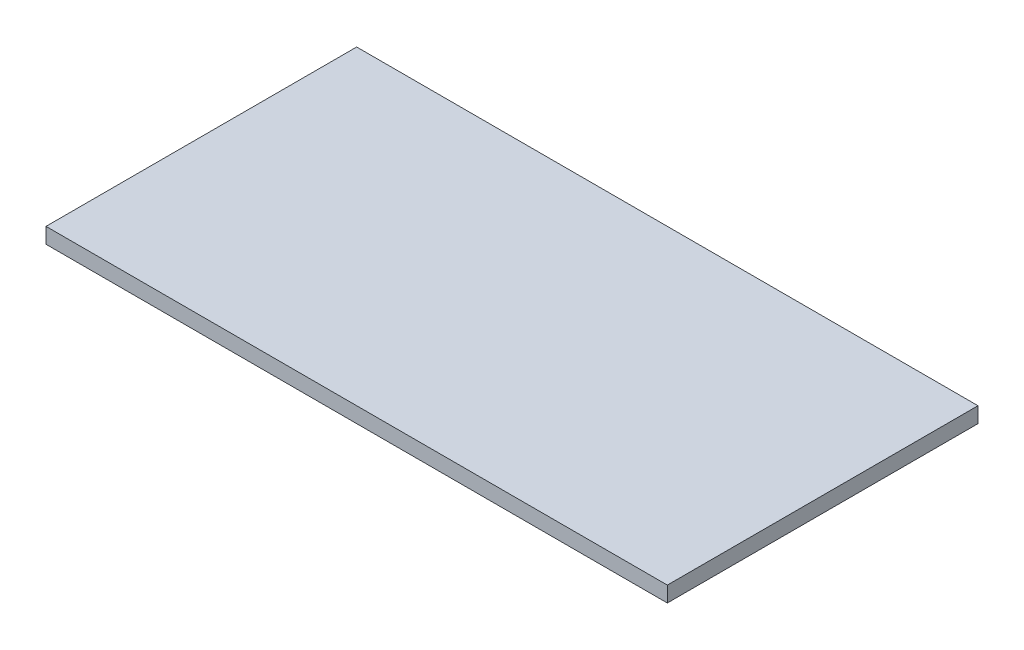
SolidWorks part; units mm, degrees
ref_plane "Front Plane" through (0, 0, 0) normal (0, 0, 1) x (1, 0, 0)
ref_plane "Top Plane" through (0, 0, 0) normal (0, 1, 0) x (1, 0, 0)
ref_plane "Right Plane" through (0, 0, 0) normal (1, 0, 0) x (0, 0, -1)
sketch "Sketch1" plane through (0, 0, 0) normal (0, 1, 0) x (1, 0, 0)
  line L1 (127, -63.5) -> (-127, -63.5)
  line L2 (127, -63.5) -> (127, 63.5)
  line L3 (127, 63.5) -> (-127, 63.5)
  line L4 (-127, -63.5) -> (-127, 63.5)
  line L5 (127, -63.5) -> (-127, 63.5) construction
  line L6 (127, 63.5) -> (-127, -63.5) construction
  point P0 (0, 0)
  dimension "D1" = 127
  dimension "D2" = 254
extrude "Boss-Extrude1" add sketch "Sketch1" along normal blind 6.35
sketch "Sketch2" plane through (0, 0, 0) normal (0, 1, 0) x (1, 0, 0)
  line L0 (-127, 0) -> (127, 0) construction
  line L1 (-127, 63.5) -> (-127, -63.5) construction
  line L2 (127, -63.5) -> (127, 63.5) construction
  line L3 (0, 63.5) -> (0, -63.5) construction
  line L4 (127, 63.5) -> (-127, 63.5) construction
  line L5 (-127, -63.5) -> (127, -63.5) construction
  line L6 (-107.95, -63.5) -> (-107.95, -57.15)
  line L7 (-127, -50.8) -> (-120.65, -50.8)
  line L8 (-9.398, -63.5) -> (-9.398, -57.15)
  line L9 (-127, 50.8) -> (-120.65, 50.8)
  line L10 (-120.65, -50.8) -> (-120.65, -57.15)
  line L11 (-120.65, -57.15) -> (-107.95, -57.15)
  line L12 (-107.95, 63.5) -> (-107.95, 57.15)
  line L13 (-120.65, 57.15) -> (-107.95, 57.15)
  line L14 (-120.65, 57.15) -> (-120.65, 50.8)
  line L15 (-9.398, 63.5) -> (-9.398, 57.15)
  line L16 (9.398, 63.5) -> (9.398, 57.15)
  line L17 (9.398, -63.5) -> (9.398, -57.15)
  line L18 (107.95, -63.5) -> (107.95, -57.15)
  line L19 (120.65, -57.15) -> (107.95, -57.15)
  line L20 (120.65, -50.8) -> (120.65, -57.15)
  line L21 (127, -50.8) -> (120.65, -50.8)
  line L22 (127, 50.8) -> (120.65, 50.8)
  line L23 (107.95, 63.5) -> (107.95, 57.15)
  line L24 (120.65, 57.15) -> (120.65, 50.8)
  line L25 (120.65, 57.15) -> (107.95, 57.15)
  line L26 (-9.398, -57.15) -> (9.398, -57.15)
  line L27 (-9.398, 57.15) -> (9.398, 57.15)
  line L28 (-51.5722, 5.2394) -> (-23.4255, 5.2394)
  line L33 (-63.2415, -5.2394) -> (-51.5722, 5.2394) construction
  line L34 (-63.2415, 5.2394) -> (-51.5722, -5.2394) construction
  line L35 (-51.5722, -5.2394) -> (-23.4255, -5.2394)
  line L36 (-63.2415, -5.2394) -> (-91.3883, -5.2394)
  line L37 (-63.2415, 5.2394) -> (-91.3883, 5.2394)
  line L38 (-63.2415, -5.2394) -> (-63.2415, -33.8843)
  line L39 (-51.5722, -5.2394) -> (-51.5722, -33.8843)
  line L40 (-63.2415, 5.2394) -> (-63.2415, 33.8843)
  line L41 (-51.5722, 5.2394) -> (-51.5722, 33.8843)
  line L42 (63.2415, -5.2394) -> (63.2415, -33.8843)
  line L43 (63.2415, -5.2394) -> (91.3883, -5.2394)
  line L44 (51.5722, -5.2394) -> (51.5722, -33.8843)
  line L45 (51.5722, -5.2394) -> (23.4255, -5.2394)
  line L46 (51.5722, 5.2394) -> (23.4255, 5.2394)
  line L47 (51.5722, 5.2394) -> (51.5722, 33.8843)
  line L48 (63.2415, 5.2394) -> (63.2415, 33.8843)
  line L49 (63.2415, 5.2394) -> (91.3883, 5.2394)
  arc A1 (-51.5722, 33.8843) -> (-23.5071, 5.7438) centre (-57.4069, 0) cw
  arc A2 (-23.4255, -5.2394) -> (-51.3814, -33.8509) centre (-57.4069, 0) cw
  arc A3 (-63.2415, -33.8843) -> (-91.3438, -5.5205) centre (-57.4069, 0) cw
  arc A4 (-91.3883, 5.2394) -> (-63.2415, 33.8843) centre (-57.4069, 0) cw
  arc A5 (63.2415, -33.8843) -> (91.3438, -5.5205) centre (57.4069, 0) ccw
  arc A6 (23.4255, -5.2394) -> (51.3814, -33.8509) centre (57.4069, 0) ccw
  arc A7 (51.5722, 33.8843) -> (23.5071, 5.7438) centre (57.4069, 0) ccw
  arc A8 (91.3883, 5.2394) -> (63.2415, 33.8843) centre (57.4069, 0) ccw
  circle A9 centre (-57.4069, 0) radius 43.501
  circle A10 centre (-57.4069, 0) radius 34.0548
  circle A11 centre (57.4069, 0) radius 43.501
  circle A12 centre (57.4069, 0) radius 34.0548
  circle A13 centre (-57.4069, 0) radius 1.651
  circle A14 centre (57.4069, 0) radius 1.651
  dimension "D9" = 87.002
  dimension "D10" = 3.302
  dimension "D1" = 19.05
  dimension "D2" = 6.35
  dimension "D3" = 6.35
  dimension "D4" = 98.552
  dimension "D5" = 6.35
  dimension "D6" = 6.35
  dimension "D7" = 101.6
  dimension "D8" = 12.7
